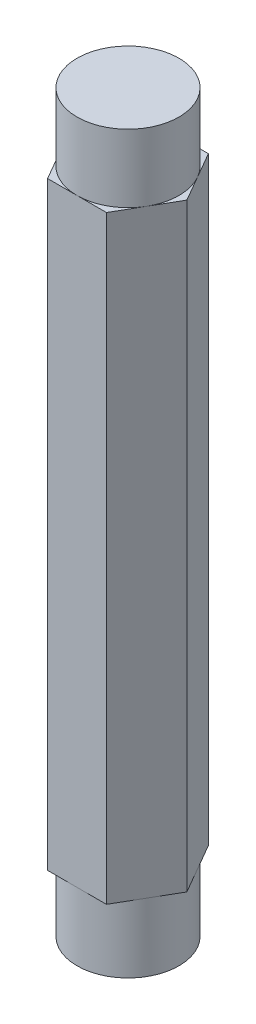
SolidWorks part; units mm, degrees
material "Alum Plate"
ref_plane "Front Plane" through (0, 0, 0) normal (0, 0, 1) x (1, 0, 0)
ref_plane "Top Plane" through (0, 0, 0) normal (0, 1, 0) x (1, 0, 0)
ref_plane "Right Plane" through (0, 0, 0) normal (1, 0, 0) x (0, 0, -1)
sketch "Sketch1" plane through (0, 0, 0) normal (0, 1, 0) x (1, 0, 0)
  line L1 (1.3748, -2.3812) -> (2.7496, 0)
  line L2 (2.7496, 0) -> (1.3748, 2.3813)
  line L3 (1.3748, 2.3813) -> (-1.3748, 2.3813)
  line L4 (-1.3748, 2.3813) -> (-2.7496, 0)
  line L5 (-2.7496, 0) -> (-1.3748, -2.3812)
  line L6 (-1.3748, -2.3812) -> (1.3748, -2.3812)
  circle A0 centre (0, 0) radius 2.3812 construction
  dimension "D1" = 4.7625
extrude "Boss-Extrude1" add sketch "Sketch1" along normal mid plane 27.9908
sketch "Sketch2" plane through (0, 13.9954, 0) normal (0, 1, 0) x (1, 0, 0)
  line L0 (1.3748, -2.3812) -> (2.7496, 0) construction
  circle A0 centre (0, 0) radius 2.3812
extrude "Boss-Extrude2" add sketch "Sketch2" along normal blind 3.175
mirror "Mirror1" about plane through (0, 0, 0) normal (0, 1, 0) of "Boss-Extrude2"
